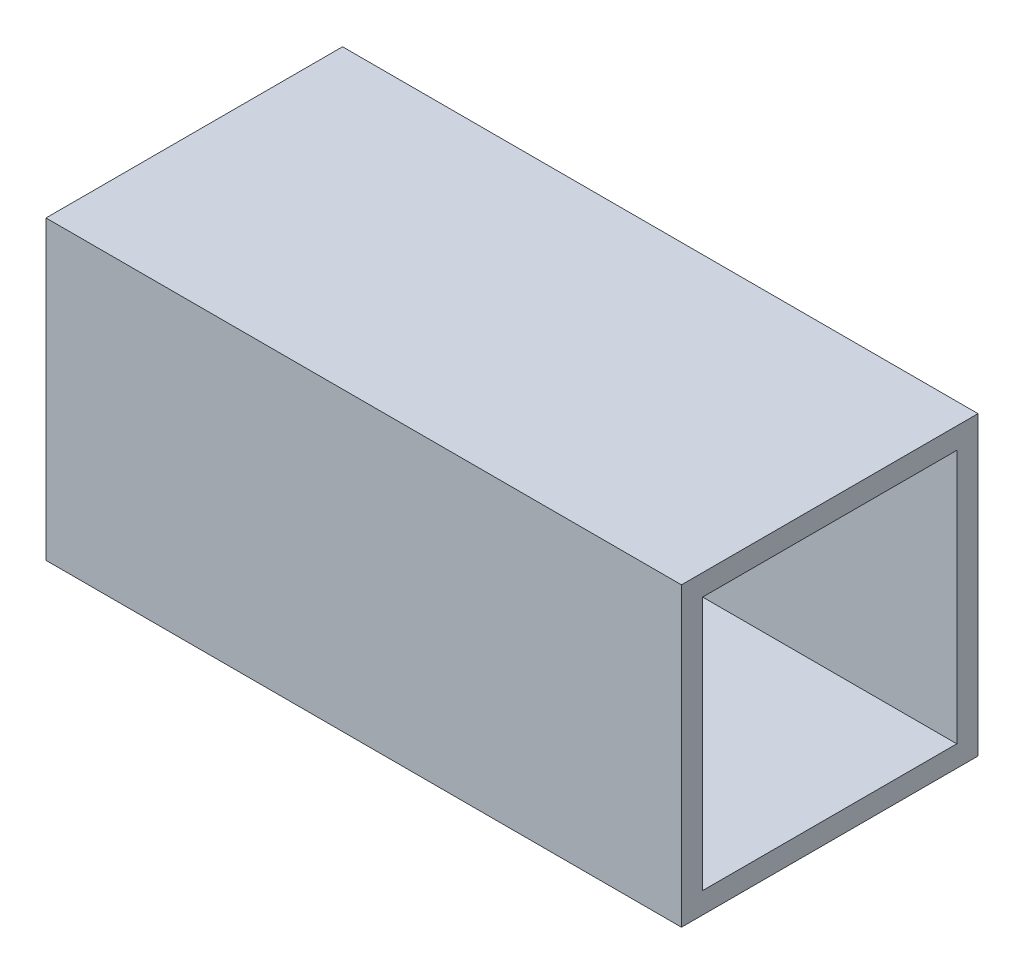
SolidWorks part; units mm, degrees
material "6061 Alloy"
ref_plane "Front Plane" through (0, 0, 0) normal (0, 0, 1) x (1, 0, 0)
ref_plane "Top Plane" through (0, 0, 0) normal (0, 1, 0) x (1, 0, 0)
ref_plane "Right Plane" through (0, 0, 0) normal (1, 0, 0) x (0, 0, -1)
sketch "Sketch1" plane through (0, 0, 0) normal (1, 0, 0) x (0, 0, -1)
  line L0 (41.275, 41.275) -> (3.175, 41.275)
  line L1 (0, 0) -> (44.45, 0)
  line L2 (44.45, 0) -> (44.45, 44.45)
  line L3 (44.45, 44.45) -> (0, 44.45)
  line L4 (0, 44.45) -> (0, 0)
  line L5 (3.175, 41.275) -> (3.175, 3.175)
  line L6 (3.175, 3.175) -> (41.275, 3.175)
  line L7 (41.275, 3.175) -> (41.275, 41.275)
  circle A0 centre (22.225, 22.225) radius 22.225 construction
  dimension "D1" = 44.45
  dimension "D2" = 3.175
extrude "Boss-Extrude1" add sketch "Sketch1" along normal mid plane 95.25
